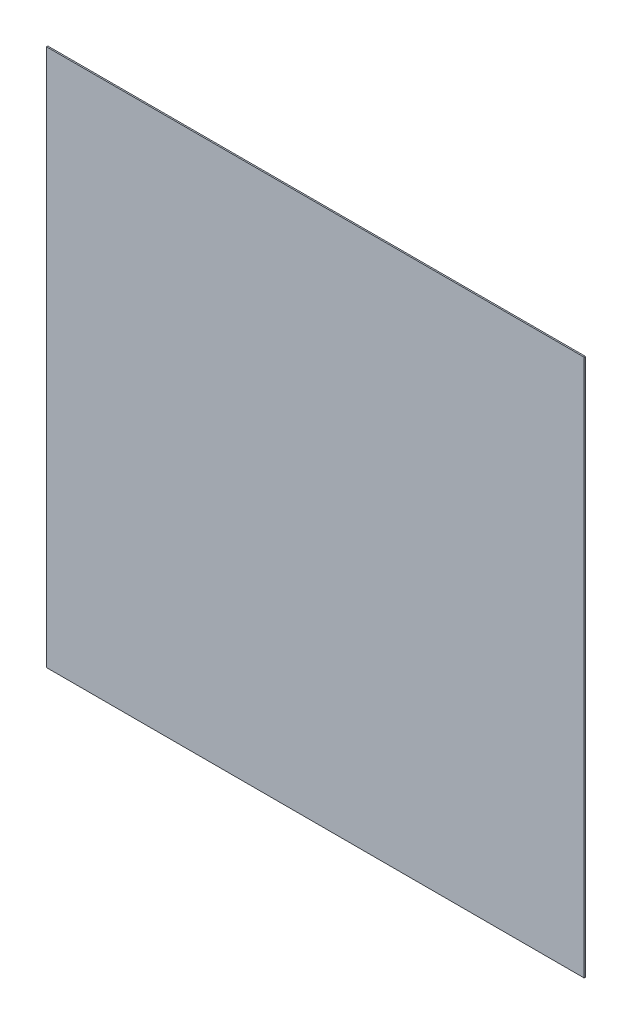
SolidWorks part; units mm, degrees
ref_plane "Front Plane" through (0, 0, 0) normal (0, 0, 1) x (1, 0, 0)
ref_plane "Top Plane" through (0, 0, 0) normal (0, 1, 0) x (1, 0, 0)
ref_plane "Right Plane" through (0, 0, 0) normal (1, 0, 0) x (0, 0, -1)
sketch "Sketch1" plane through (0, 0, 0) normal (0, 0, 1) x (1, 0, 0)
  line L1 (0, 0) -> (400, 0)
  line L2 (0, 0) -> (0, -400)
  line L3 (0, -400) -> (400, -400)
  line L4 (400, 0) -> (400, -400)
  dimension "D1" = 400
  dimension "D2" = 400
extrude "Boss-Extrude1" add sketch "Sketch1" along normal blind 1
